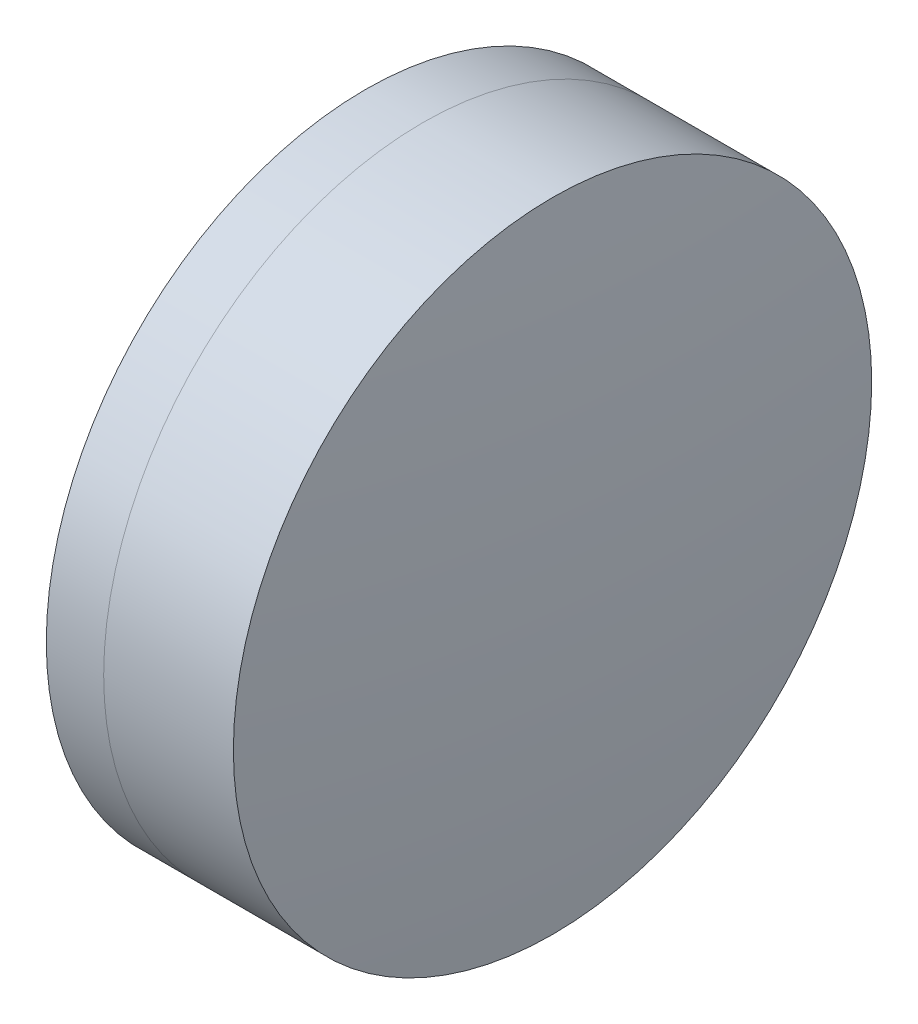
SolidWorks part; units mm, degrees
ref_plane "前视基准面" through (0, 0, 0) normal (0, 0, 1) x (1, 0, 0)
ref_plane "上视基准面" through (0, 0, 0) normal (0, 1, 0) x (1, 0, 0)
ref_plane "右视基准面" through (0, 0, 0) normal (1, 0, 0) x (0, 0, -1)
sketch "草图1" plane through (0, 0, 0) normal (0, 1, 0) x (1, 0, 0)
  line L0 (124.5233, 0) -> (395.1269, 0) construction
  line L1 (297.9168, -25.4) -> (302.4825, -25.4)
  line L2 (297.9168, 25.4) -> (302.4825, 25.4)
  arc A0 (302.4825, -25.4) -> (302.4825, 25.4) centre (269.4109, 0) ccw
  arc A1 (297.9168, 25.4) -> (297.9168, -25.4) centre (341.9109, 0) ccw
  point P10 (291.1109, 0)
  point P11 (311.1109, 0)
  dimension "D3" = 50.8
  dimension "D4" = 41.7
  dimension "D1" = 25.4
  dimension "D2" = 25.4
  dimension "D5" = 20
revolve "旋转1" add sketch "草图1" angle 360 about L0
sketch "草图2" plane through (0, 0, 0) normal (0, 1, 0) x (1, 0, 0)
  line L0 (-0.5519, 0) -> (409.4962, 0) construction
  line L2 (302.4825, 25.4) -> (312.8052, 25.4)
  line L3 (302.4825, -25.4) -> (312.8052, -25.4)
  arc A0 (312.8052, -25.4) -> (312.8052, 25.4) centre (66.4109, 0) ccw
  arc A1 (302.4825, -25.4) -> (302.4825, 25.4) centre (269.4109, 0) ccw construction
  arc A2 (302.4825, -25.4) -> (302.4825, 25.4) centre (269.4109, 0) ccw
  point P4 (311.1109, 0)
  point P8 (314.1109, 0)
  dimension "D1" = 247.7
  dimension "D2" = 3
revolve "旋转3" add sketch "草图2" angle 360 about L0
